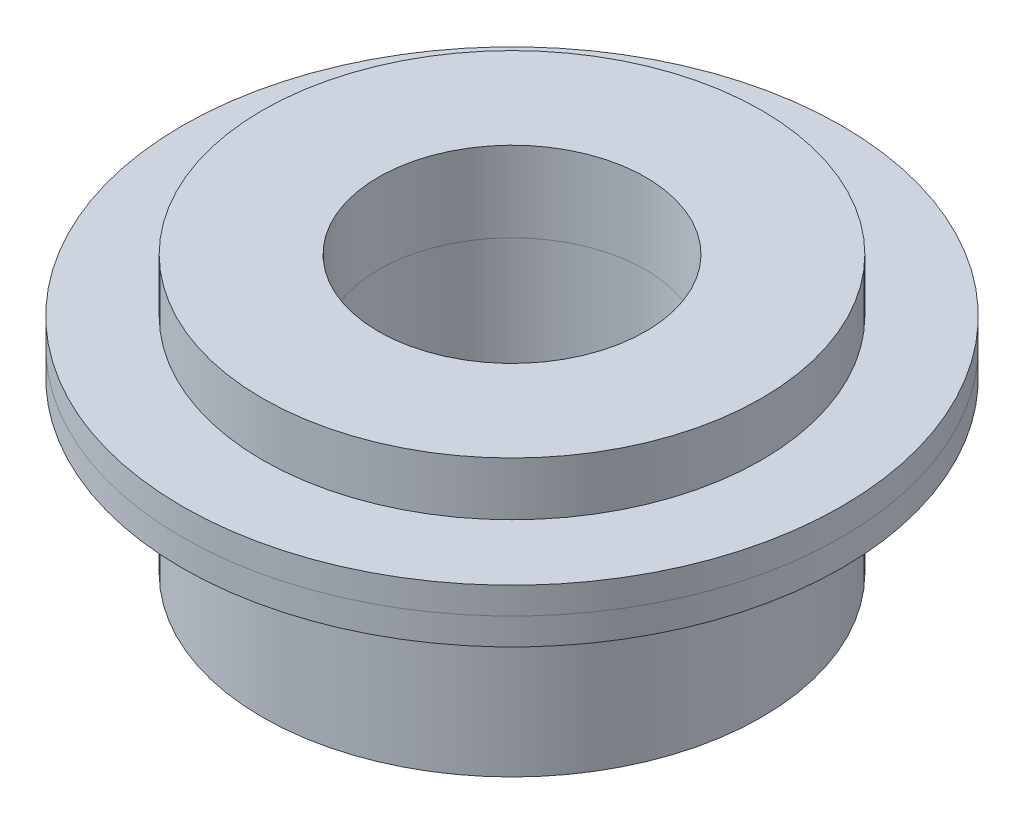
SolidWorks part; units mm, degrees
ref_plane "Front Plane" through (0, 0, 0) normal (0, 0, 1) x (1, 0, 0)
ref_plane "Top Plane" through (0, 0, 0) normal (0, 1, 0) x (1, 0, 0)
ref_plane "Right Plane" through (0, 0, 0) normal (1, 0, 0) x (0, 0, -1)
sketch "Sketch2" plane through (0, 0, 0) normal (0, 1, 0) x (1, 0, 0)
  circle A0 centre (0, 0) radius 14
  dimension "D1" = 28
extrude "Boss-Extrude1" add sketch "Sketch2" along normal blind 9.5
sketch "Sketch3" plane through (0, 9.5, 0) normal (0, 1, 0) x (1, 0, 0)
  circle A0 centre (0, 0) radius 18.5
  dimension "D1" = 37
extrude "Boss-Extrude2" add sketch "Sketch3" along normal blind 1.5
sketch "Sketch4" plane through (0, 11, 0) normal (0, 1, 0) x (1, 0, 0)
  circle A0 centre (0, 0) radius 18.5
  dimension "D1" = 37
extrude "Boss-Extrude5" add sketch "Sketch4" along normal blind 1.5 separate body
sketch "Sketch7" plane through (0, 12.5, 0) normal (0, 1, 0) x (1, 0, 0)
  circle A0 centre (0, 0) radius 14
  dimension "D1" = 28
extrude "Boss-Extrude6" add sketch "Sketch7" along normal blind 3
sketch "Sketch8" plane through (0, 15.5, 0) normal (0, 1, 0) x (1, 0, 0)
  circle A0 centre (0, 0) radius 7.5
  dimension "D1" = 15
extrude "Cut-Extrude2" cut sketch "Sketch8" against normal through all
